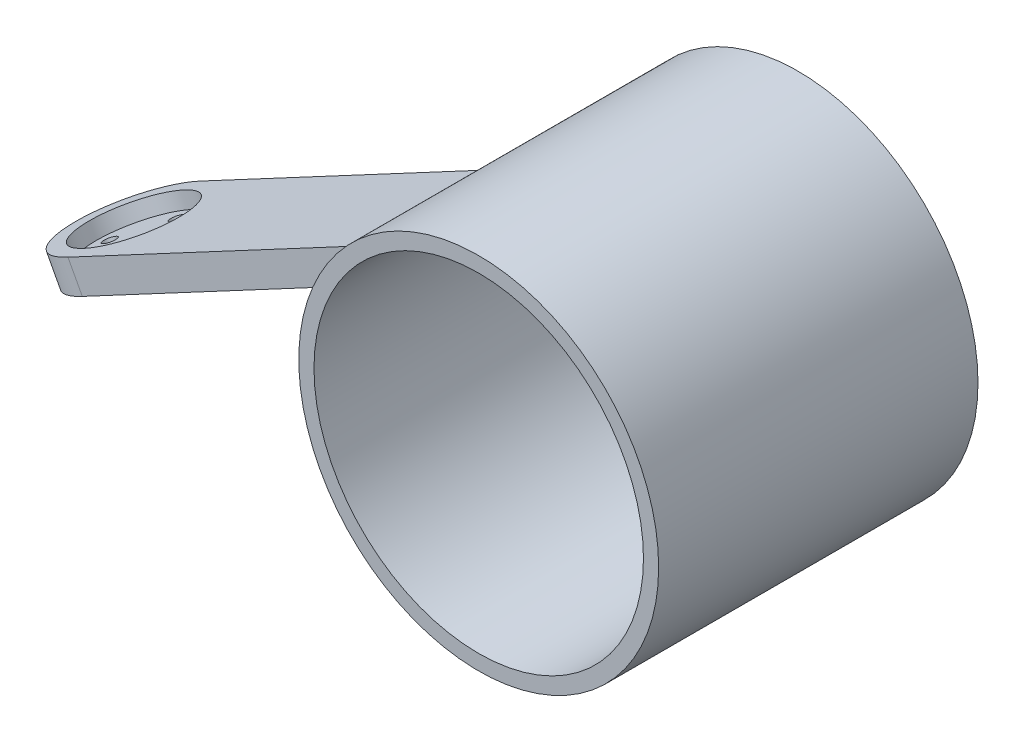
SolidWorks part; units mm, degrees
ref_plane "Front Plane" through (0, 0, 0) normal (0, 0, 1) x (1, 0, 0)
ref_plane "Top Plane" through (0, 0, 0) normal (0, 1, 0) x (1, 0, 0)
ref_plane "Right Plane" through (0, 0, 0) normal (1, 0, 0) x (0, 0, -1)
sketch "Sketch1" plane through (0, 0, 0) normal (0, 0, 1) x (1, 0, 0)
  circle A0 centre (0, 0) radius 32.5
  circle A1 centre (0, 0) radius 35.5
  dimension "D1" = 65
  dimension "D2" = 71
extrude "Boss-Extrude1" add sketch "Sketch1" along normal blind 63
sketch "Sketch2" plane through (0, 0, 0) normal (0, 0, -1) x (-1, 0, 0)
  circle A0 centre (0, 0) radius 32.5
extrude "Boss-Extrude2" add sketch "Sketch2" against normal blind 3
ref_plane "Plane1" through (-10.5747, 19.826, 0) normal (0.4706, -0.8823, 0) x (0, 0, -1)
ref_plane "Plane2" through (0, 0, 26.897) normal (0, 0, 1) x (1, 0, 0)
sketch "Sketch6" plane through (0, 0, 26.897) normal (0, 0, 1) x (1, 0, 0)
  line L1 (-34.2089, 9.4868) -> (-102.8573, -27.1286)
  line L2 (-35.442, 2.029) -> (-100.0336, -32.4226)
  line L3 (-102.8573, -27.1286) -> (-100.0336, -32.4226)
  circle A0 centre (0, 0) radius 35.5 construction
  circle A2 centre (0, 0) radius 35.5
  arc A3 (-34.2089, 9.4868) -> (-35.442, 2.029) centre (0, 0) ccw
  dimension "D1" = 6
  dimension "D3" = 34.2089
  dimension "D4" = 35.442
  dimension "D5" = 100.0336
  dimension "D2" = 0
extrude "Boss-Extrude6" add sketch "Sketch6" along normal blind 14.275 and the other way blind 11.725
sketch "Sketch7" plane through (-8.6922, 16.2966, 0) normal (0.4706, -0.8823, 0) x (0.8823, 0.4706, 0)
  line L0 (-30.3169, 15.172) -> (-30.3169, 41.172) construction
  circle A0 centre (-103.522, 28.172) radius 13
  dimension "D1" = 26
  dimension "D2" = 73.2051
  dimension "D3" = 13
extrude "Boss-Extrude7" add sketch "Sketch7" against normal blind 6
sketch "Sketch8" plane through (-11.5159, 21.5907, 0) normal (-0.4706, 0.8823, 0) x (0.8823, 0.4706, 0)
  circle A0 centre (-103.522, -28.172) radius 10
  arc A1 (-103.522, -15.172) -> (-103.522, -41.172) centre (-103.522, -28.172) ccw construction
  dimension "D1" = 20
extrude "Cut-Extrude1" cut sketch "Sketch8" against normal blind 3
sketch "Sketch9" plane through (-8.6922, 16.2966, 0) normal (0.4706, -0.8823, 0) x (0.8823, 0.4706, 0)
  line L0 (-103.522, 46.1825) -> (-103.522, 10.1615) construction
  line L1 (-124.845, 28.172) -> (-82.1991, 28.172) construction
  line L2 (-103.522, 41.172) -> (-30.3169, 41.172) construction
  circle A0 centre (-103.522, 35.172) radius 1.275
  circle A3 centre (-110.522, 28.172) radius 1.275
  circle A4 centre (-96.522, 28.172) radius 1.275
  circle A5 centre (-103.522, 21.172) radius 1.275
  arc A6 (-103.522, 41.172) -> (-103.522, 15.172) centre (-103.522, 28.172) ccw construction
  point P18 (-103.522, 28.172)
  dimension "D1" = 2.55
  dimension "D2" = 2.55
  dimension "D3" = 7
  dimension "D4" = 7
extrude "Cut-Extrude2" cut sketch "Sketch9" against normal through all
sketch "Sketch10" plane through (-8.6922, 16.2966, 0) normal (0.4706, -0.8823, 0) x (0.8823, 0.4706, 0)
  line L0 (-20.1059, 63) -> (24.8941, 63)
  line L1 (-20.1059, 63) -> (-20.1059, 23)
  line L2 (24.8941, 63) -> (24.8941, 23)
  line L3 (-20.1059, 23) -> (24.8941, 23)
  line L7 (32.5, 63) -> (-32.5, 63) construction
  circle A0 centre (-103.522, 35.172) radius 1.275 construction
  dimension "D1" = 45
  dimension "D2" = 40
  dimension "D3" = 83.4161
extrude "Cut-Extrude3" [suppressed] cut sketch "Sketch10" along normal through all
